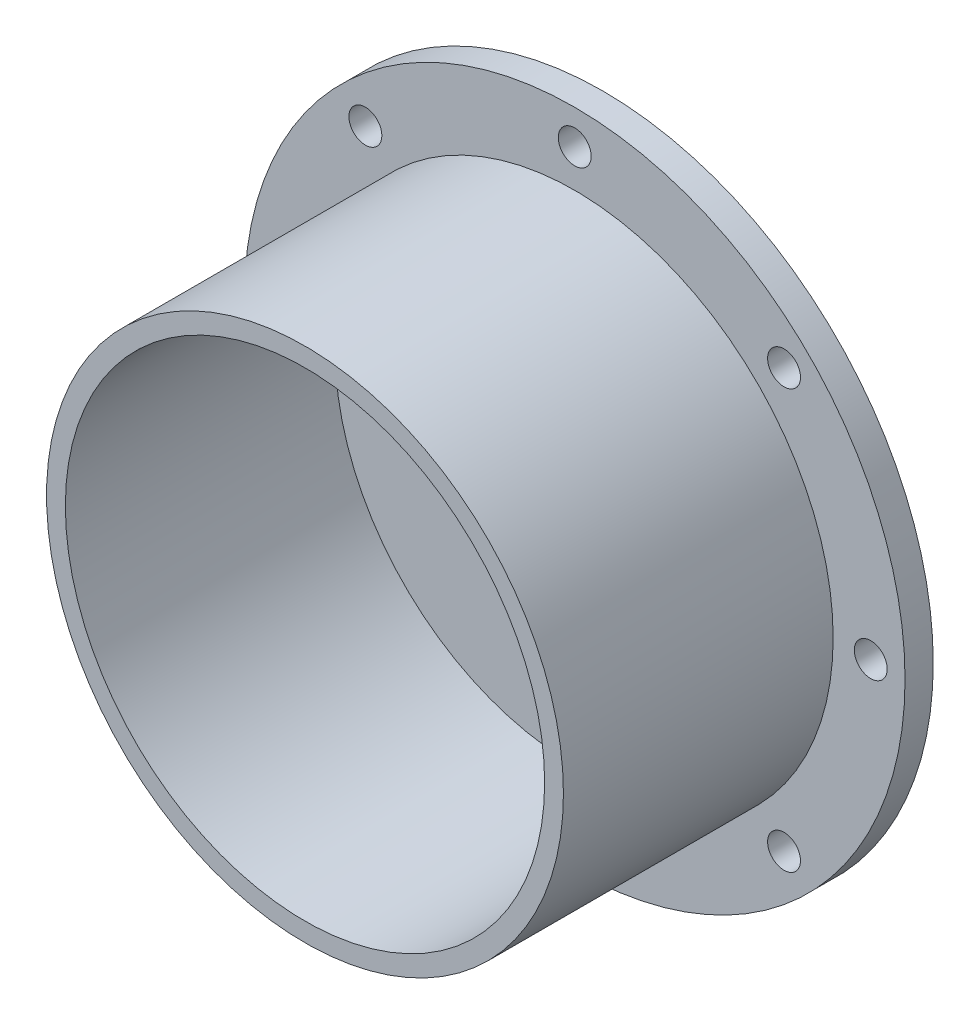
SolidWorks part; units mm, degrees
ref_plane "Front Plane" through (0, 0, 0) normal (0, 0, 1) x (1, 0, 0)
ref_plane "Top Plane" through (0, 0, 0) normal (0, 1, 0) x (1, 0, 0)
ref_plane "Right Plane" through (0, 0, 0) normal (1, 0, 0) x (0, 0, -1)
sketch "Sketch1" plane through (0, 0, 0) normal (0, 0, 1) x (1, 0, 0)
  circle A0 centre (0, 0) radius 35.15
  circle A1 centre (0, 0) radius 19.5154 construction
  circle A2 centre (0, 31.5) radius 1.75
  circle A3 centre (22.2739, 22.2739) radius 1.75
  circle A4 centre (31.5, 0) radius 1.75
  circle A5 centre (22.2739, -22.2739) radius 1.75
  circle A6 centre (0, -31.5) radius 1.75
  circle A7 centre (-22.2739, -22.2739) radius 1.75
  circle A8 centre (-31.5, 0) radius 1.75
  circle A9 centre (-22.2739, 22.2739) radius 1.75
  point P6 (0, 0)
  point P21 (0, 0)
  dimension "D1" = 70.3
  dimension "D2" = 3.5
  dimension "D3" = 31.5
  dimension "D4" = 8
extrude "Boss-Extrude2" add sketch "Sketch1" along normal blind 3
sketch "Sketch3" plane through (0, 0, 3) normal (0, 0, 1) x (1, 0, 0)
  circle A0 centre (0, 0) radius 27.5
  circle A1 centre (0, 0) radius 25.5
  point P3 (0, 0)
  dimension "D1" = 55
  dimension "D2" = 51
extrude "Boss-Extrude3" add sketch "Sketch3" along normal blind 28.7
